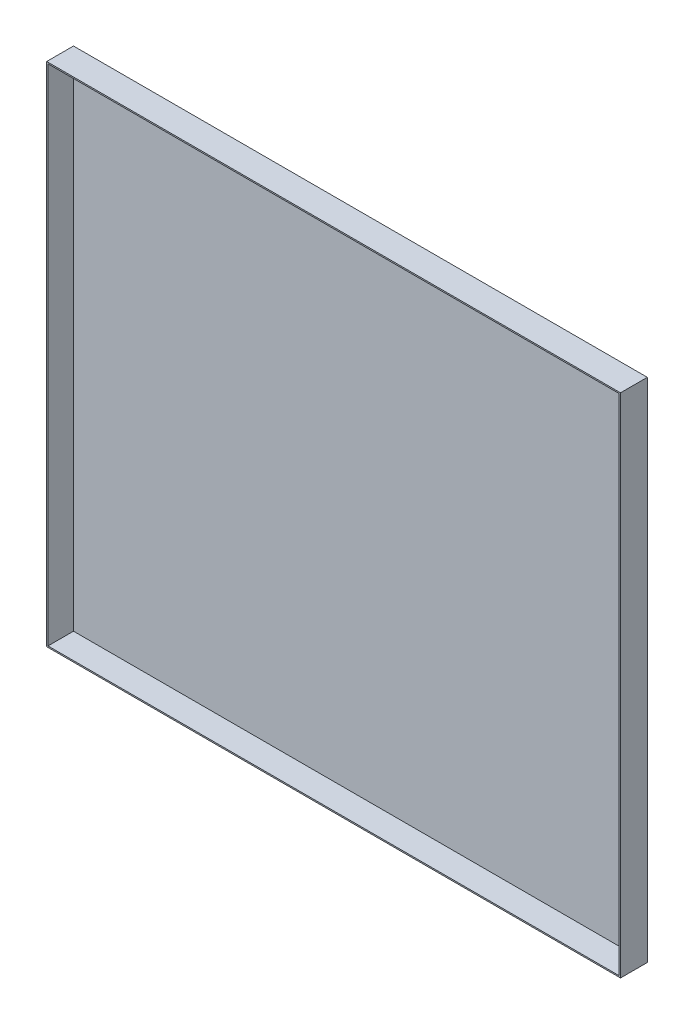
SolidWorks part; units mm, degrees
ref_plane "前视基准面" through (0, 0, 0) normal (0, 0, 1) x (1, 0, 0)
ref_plane "上视基准面" through (0, 0, 0) normal (0, 1, 0) x (1, 0, 0)
ref_plane "右视基准面" through (0, 0, 0) normal (1, 0, 0) x (0, 0, -1)
sketch "草图1" plane through (0, 0, 0) normal (0, 0, 1) x (1, 0, 0)
  line L1 (-214, 189) -> (214, 189)
  line L2 (-214, 189) -> (-214, -189)
  line L3 (-214, -189) -> (214, -189)
  line L4 (214, 189) -> (214, -189)
  line L5 (-214, 189) -> (214, -189) construction
  line L6 (-214, -189) -> (214, 189) construction
  point P0 (0, 0)
  dimension "D1" = 428
  dimension "D2" = 378
extrude "凸台-拉伸1" add sketch "草图1" along normal blind 20
shell "抽壳1" thickness 1
